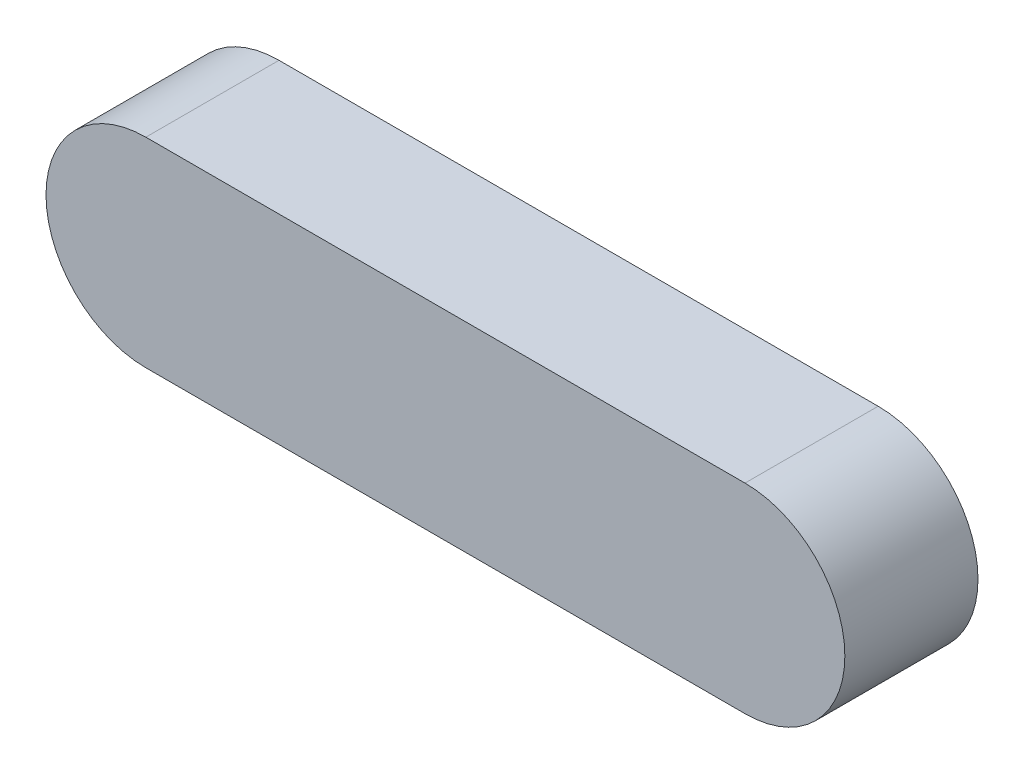
SolidWorks part; units mm, degrees
ref_plane "Front Plane" through (0, 0, 0) normal (0, 0, 1) x (1, 0, 0)
ref_plane "Top Plane" through (0, 0, 0) normal (0, 1, 0) x (1, 0, 0)
ref_plane "Right Plane" through (0, 0, 0) normal (1, 0, 0) x (0, 0, -1)
sketch "Sketch2" plane through (0, 0, 0) normal (0, 0, 1) x (1, 0, 0)
  line L0 (-3.619, 0) -> (32.381, 0) construction
  line L1 (-3.619, 6) -> (32.381, 6)
  line L2 (-3.619, -6) -> (32.381, -6)
  arc A0 (-3.619, 6) -> (-3.619, -6) centre (-3.619, 0) ccw
  arc A1 (32.381, -6) -> (32.381, 6) centre (32.381, 0) ccw
  point P3 (14.381, 0)
  dimension "D1" = 6
  dimension "D2" = 36
extrude "Boss-Extrude1" add sketch "Sketch2" along normal blind 8
